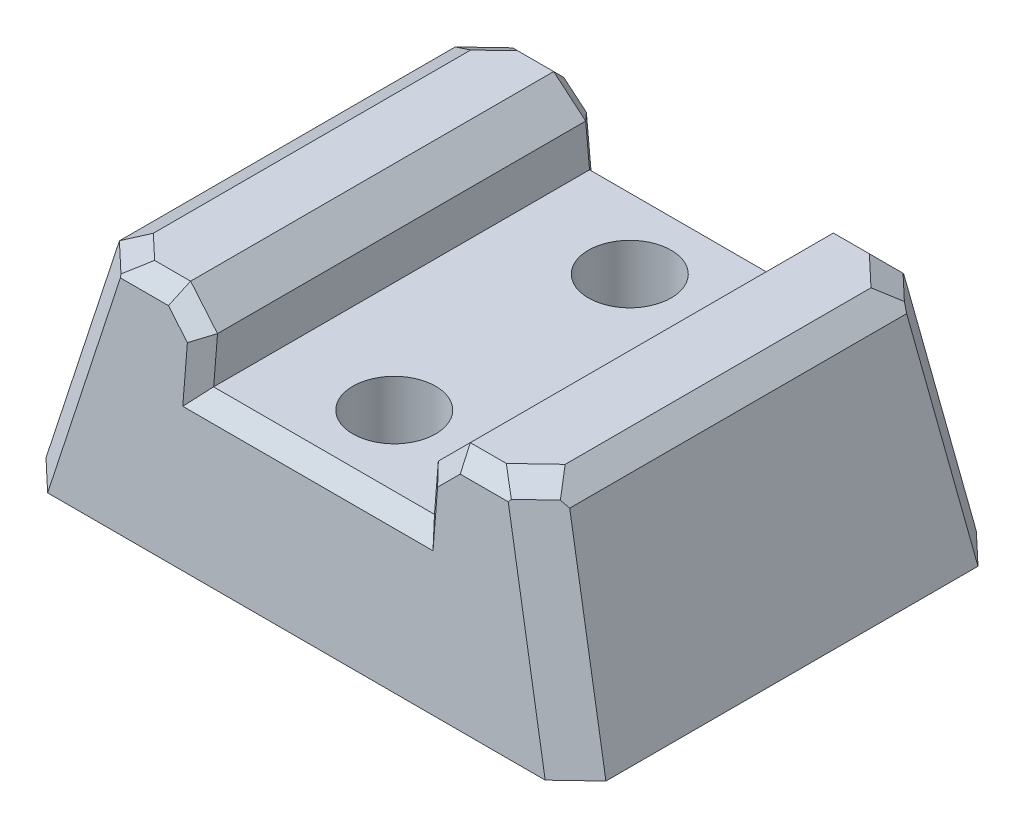
SolidWorks part; units mm, degrees
material "PET"
ref_plane "Front Plane" through (0, 0, 0) normal (0, 0, 1) x (1, 0, 0)
ref_plane "Top Plane" through (0, 0, 0) normal (0, 1, 0) x (1, 0, 0)
ref_plane "Right Plane" through (0, 0, 0) normal (1, 0, 0) x (0, 0, -1)
sketch "Sketch1" plane through (0, 0, 0) normal (0, 0, 1) x (1, 0, 0)
  line L0 (133.5295, -12.7) -> (114.4795, -12.7) construction
  line L1 (143.0545, -6.35) -> (140.5145, -6.35) construction
  line L2 (140.5145, -6.35) -> (136.0695, -6.35) construction
  line L3 (133.5295, -8.89) -> (136.0695, -6.35) construction
  line L4 (133.5295, -8.89) -> (133.5295, -12.7) construction
  line L5 (107.4945, -6.35) -> (104.9545, -6.35) construction
  line L6 (111.9395, -6.35) -> (107.4945, -6.35) construction
  line L7 (111.9395, -6.35) -> (114.4795, -8.89) construction
  line L8 (114.4795, -12.7) -> (114.4795, -8.89) construction
  line L9 (133.5295, -12.7) -> (114.4795, -12.7)
  line L10 (143.0545, -6.35) -> (140.5145, -6.35)
  line L11 (140.5145, -6.35) -> (136.0695, -6.35)
  line L12 (133.5295, -8.89) -> (136.0695, -6.35)
  line L13 (133.5295, -8.89) -> (133.5295, -12.7)
  line L14 (107.4945, -6.35) -> (104.9545, -6.35)
  line L15 (111.9395, -6.35) -> (107.4945, -6.35)
  line L16 (111.9395, -6.35) -> (114.4795, -8.89)
  line L17 (114.4795, -12.7) -> (114.4795, -8.89)
  line L18 (104.9545, -6.35) -> (104.9545, -25.4)
  line L19 (104.9545, -25.4) -> (143.0545, -25.4)
  line L20 (143.0545, -25.4) -> (143.0545, -6.35)
  line L21 (93.4545, -25.4) -> (154.5545, -25.4) construction
extrude "Boss-Extrude1" add sketch "Sketch1" against normal up to surface (33.8676 mm away)
hole_wizard "1/4 Clearance Hole1" positions "Sketch2" profile "Sketch3" hole size "1/4" standard "ANSI Inch" end condition through all
sketch "Sketch2" plane through (0, -12.7, 0) normal (0, 1, 0) x (1, 0, 0)
  point P0 (124.0045, 6.7738)
  point P3 (124.0045, 27.0938)
sketch "Sketch3" plane through (124.0045, -12.7, -6.7738) normal (1, 0, 0) x (0, 0, 1)
  line L0 (0, 0) -> (0, 12.7)
  line L1 (0, 12.7) -> (3.5712, 12.7)
  line L2 (3.5712, 12.7) -> (3.5712, 0)
  line L5 (3.5712, 0) -> (0, 0)
  line L11 (0, -6.35) -> (0, 107.95) construction
  dimension "Thru Hole Dia." = 7.1425
  dimension "Thru Hole Depth" = 12.7
draft "Draft1" type of draft neutral plane draft angle 15 faces to draft 1 face at (143.0545, -15.875, -16.9338) neutral plane through (140.5145, -6.35, -76.4647) neutral plane normal (0, 1, 0) parameters "D1"=15
draft "Draft2" type of draft neutral plane draft angle 15 faces to draft 1 face at (104.9545, -15.875, -16.9338) neutral plane through (140.5145, -6.35, -76.4647) neutral plane normal (0, 1, 0) parameters "D1"=15
draft "Draft3" type of draft neutral plane draft angle 5 faces to draft 1 face at (124.0045, -11.938, 0) neutral plane through (140.5145, -6.35, -76.4647) neutral plane normal (0, 1, 0) parameters "D1"=5
draft "Draft4" type of draft neutral plane draft angle 5 faces to draft 1 face at (124.0045, -11.938, -33.8676) neutral plane through (140.5145, -6.35, -76.4647) neutral plane normal (0, 1, 0) parameters "D1"=5
chamfer "Chamfer1" distance 2.54 angle 45 4 edges at (102.4022, -15.875, -34.7009) (145.6067, -15.875, -34.7009) (102.4022, -15.875, 0.8333) (145.6067, -15.875, 0.8333)
chamfer "Chamfer2" distance 1.27 angle 45 20 edges at (133.5295, -10.795, -34.2565) (134.7995, -7.62, -33.9787) (138.2168, -6.35, -33.8676) (141.7093, -6.35, -32.5931) (143.0545, -6.35, -16.9338) (141.7093, -6.35, -1.2745) (138.2168, -6.35, 0) (134.7995, -7.62, 0.1111) (133.5295, -10.795, 0.3889) (124.0045, -12.7, 0.5556) (124.0045, -12.7, -34.4231) (114.4795, -10.795, -34.2565) (113.2095, -7.62, -33.9787) (109.7921, -6.35, -33.8676) (106.2996, -6.35, -32.5931) (104.9545, -6.35, -16.9338) (106.2996, -6.35, -1.2745) (109.7921, -6.35, 0) (113.2095, -7.62, 0.1111) (114.4795, -10.795, 0.3889)
hole_wizard "Hole1" positions "Sketch4" profile "Sketch5" legacy
sketch "Sketch4" plane through (0, -25.4, 0) normal (0, -1, 0) x (-1, 0, 0)
  line L1 (-124.0045, 35.5342) -> (-124.0045, -1.6667) construction
  line L2 (-145.4686, 35.5342) -> (-102.5403, 35.5342) construction
  line L3 (-102.5403, -1.6667) -> (-145.4686, -1.6667) construction
  line L5 (-124.0045, 16.9338) -> (-148.1589, 16.9338) construction
  line L6 (-148.1589, 32.9852) -> (-148.1589, 0.8824) construction
  point P19 (-136.0817, 16.9338)
  point P22 (-111.9272, 16.9338)
sketch "Sketch5" plane through (111.9272, -25.4, -16.9338) normal (1, 0, 0) x (0, 0, -1)
  line L0 (0, 0) -> (0, 4.699)
  line L1 (0, 4.699) -> (2.8702, 4.699)
  line L2 (2.8702, 4.699) -> (2.9972, 0)
  line L3 (2.9972, 0) -> (0, 0)
  line L4 (0, 110) -> (0, -10) construction
  dimension "Minor Diameter" = 5.7404
  dimension "Depth" = 4.699
  dimension "Major Diameter" = 5.9944
hole_wizard "#8 Clearance Hole1" positions "Sketch6" profile "Sketch7" hole size "#8" standard "ANSI Inch"
sketch "Sketch6" plane through (0, -25.4, 0) normal (0, -1, 0) x (-1, 0, 0)
  point P0 (-136.0817, 16.9338)
  point P3 (-111.9272, 16.9338)
sketch "Sketch7" plane through (136.0817, -25.4, -16.9338) normal (1, 0, 0) x (0, 0, -1)
  line L0 (0, 0) -> (0, 11.0016)
  line L1 (0, 11.0016) -> (2.4574, 9.525)
  line L2 (2.4574, 9.525) -> (2.4574, 0)
  line L5 (2.4574, 0) -> (0, 0)
  line L10 (0, 11.0016) -> (-2.4575, 9.525) construction
  line L11 (0, -6.35) -> (0, 107.95) construction
  dimension "Hole Dia." = 4.9149
  dimension "Hole Depth" = 9.525
  dimension "Drill Angle" = 118
